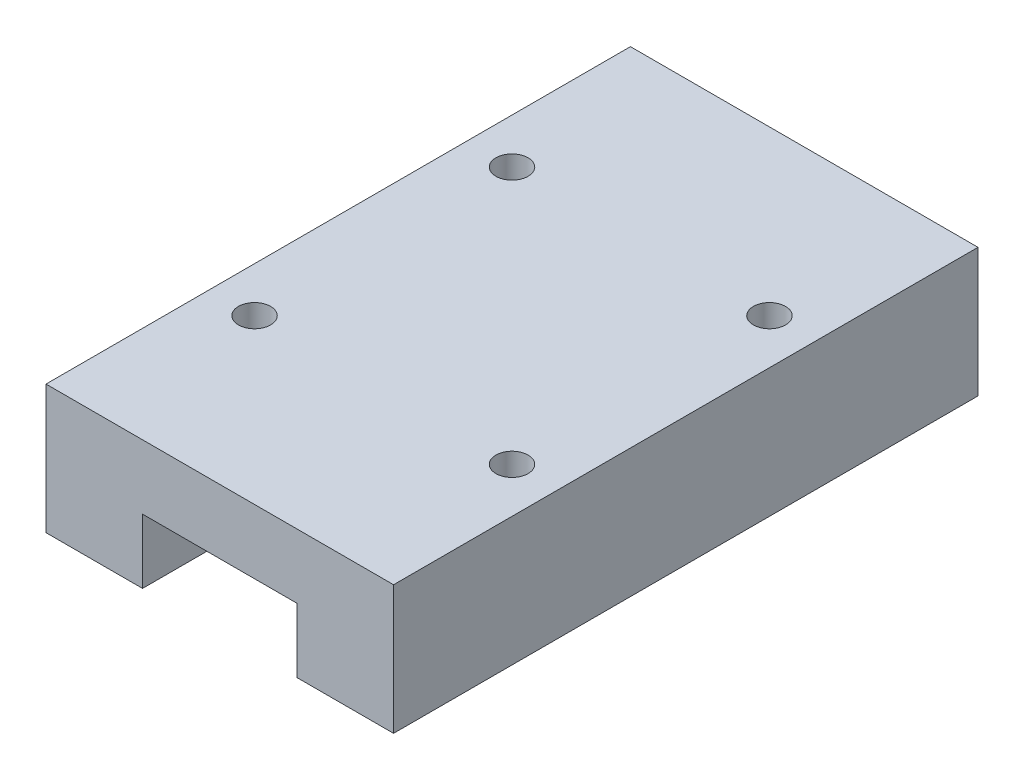
SolidWorks part; units mm, degrees
ref_plane "Front" through (0, 0, 0) normal (0, 0, 1) x (1, 0, 0)
ref_plane "Top" through (0, 0, 0) normal (0, 1, 0) x (1, 0, 0)
ref_plane "Right" through (0, 0, 0) normal (1, 0, 0) x (0, 0, -1)
sketch "Sketch2" plane through (0, 0, 0) normal (0, 0, 1) x (1, 0, 0)
  line L0 (0, 0) -> (0, 10)
  line L1 (0, 10) -> (27, 10)
  line L2 (27, 10) -> (27, 0)
  line L3 (27, 0) -> (19.5, 0)
  line L4 (19.5, 0) -> (19.5, 5)
  line L5 (19.5, 5) -> (7.5, 5)
  line L6 (7.5, 5) -> (7.5, 0)
  line L7 (7.5, 0) -> (0, 0)
  dimension "D1" = 27
  dimension "D2" = 10
  dimension "D3" = 7.5
  dimension "D4" = 5
extrude "Boss-Extrude1" add sketch "Sketch2" along normal blind 45.4
hole_wizard "M3x0.5 Tapped Hole1" positions "Sketch3" profile "Sketch4" tap size "M3x0.5" standard "ANSI Metric"
sketch "Sketch3" plane through (0, 10, 0) normal (0, 1, 0) x (1, 0, 0)
  line L0 (0, -22.7) -> (27, -22.7) construction
  line L1 (0, -45.4) -> (0, 0) construction
  line L2 (27, -45.4) -> (27, 0) construction
  line L5 (13.5, 0) -> (13.5, -45.4) construction
  line L6 (27, 0) -> (0, 0) construction
  line L7 (27, -45.4) -> (0, -45.4) construction
  point P16 (3.5, -12.7)
  point P18 (3.5, -32.7)
  point P20 (23.5, -32.7)
  point P22 (23.5, -12.7)
  dimension "D1" = 20
  dimension "D2" = 20
  dimension "D3" = 10
  dimension "D4" = 10
  dimension "D5" = 20
  dimension "D6" = 20
  dimension "D7" = 10
cosmetic thread "Hole Thread1"
cosmetic thread "Hole Thread2"
cosmetic thread "Hole Thread3"
cosmetic thread "Hole Thread4"
sketch "Sketch4" plane through (23.5, 10, 12.7) normal (1, 0, 0) x (0, 0, 1)
  line L0 (0, 0) -> (0, 6.7511)
  line L1 (0, 6.7511) -> (1.25, 6)
  line L2 (1.25, 6) -> (1.25, 0)
  line L5 (1.25, 0) -> (0, 0)
  line L10 (0, 6.7511) -> (-1.25, 6) construction
  line L11 (0, -6.35) -> (0, 107.95) construction
  dimension "Tap Drill Dia." = 2.5
  dimension "Tap Drill Depth" = 6
  dimension "Drill Angle" = 118
sketch "Sketch5" plane through (0, 10, 0) normal (0, 1, 0) x (1, 0, 0)
  circle A0 centre (23.5, -32.7) radius 3
  circle A1 centre (23.5, -12.7) radius 3
  circle A2 centre (3.5, -12.7) radius 3
  circle A3 centre (3.5, -32.7) radius 3
  circle A4 centre (3.5, -12.7) radius 2.85
  circle A5 centre (23.5, -12.7) radius 2.85
  circle A6 centre (3.5, -32.7) radius 2.85
  circle A7 centre (23.5, -32.7) radius 2.85
  dimension "D1" = 6
  dimension "D2" = 5.7
equation "\"D5@Sketch3\"=\"D1@Sketch3\""
equation "\"D7@Sketch3\"=\"D4@Sketch3\""
equation "\"D4@Sketch3\"=\"D1@Sketch3\"/2"
